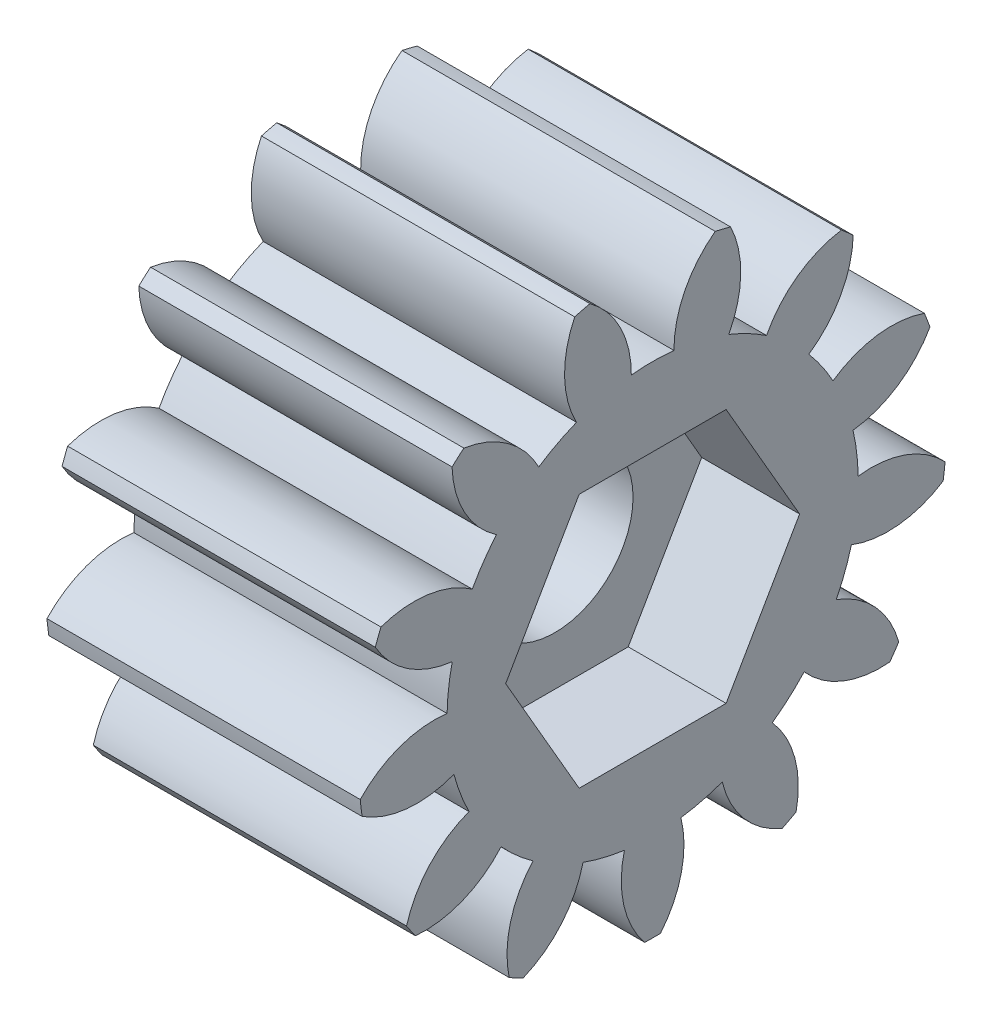
SolidWorks part; units mm, degrees
ref_plane "Plane1" through (0, 0, 0) normal (0, 0, 1) x (1, 0, 0)
ref_plane "Plane2" through (0, 0, 0) normal (0, 1, 0) x (1, 0, 0)
ref_plane "Plane3" through (0, 0, 0) normal (1, 0, 0) x (0, 0, -1)
sketch "HoldingSke" plane through (0, 0, 0) normal (0, 1, 0) x (1, 0, 0)
  line L0 (0, 0) -> (0.4872, -0.1125)
  line L1 (-15, 0) -> (100, 0) construction
  line L2 (0, 0) -> (-2.1039, 2.3779)
  line L3 (0, 0) -> (-11.863, 4.5341)
  line L4 (0, 0) -> (8.4147, 1.9427)
  line L5 (0, 0) -> (-46.8476, -17.4728)
  line L6 (0, 0) -> (-13.2634, -8.9489)
  line L7 (-2.1039, 2.3779) -> (8.6586, 51.2059)
  line L8 (-76.2, 54.61) -> (-74.8, 54.61)
  line L9 (-71.009, 38.7566) -> (-53.1078, 45.2721)
  line L10 (-76.2, 71.12) -> (104.1128, 71.12)
  line L11 (0, 0) -> (-16, 0)
  line L12 (-76.2, 101.6) -> (-76.133, 101.6)
  line L13 (24.9733, 27.94) -> (52.9518, 28.4284)
  line L14 (24.9733, 27.94) -> (24.9743, 27.94)
  line L15 (24.9733, 27.94) -> (100.4006, 29.5858)
  line L16 (-63.627, -2) -> (-12.827, -2)
  circle A0 centre (0, 0) radius 4
  circle A1 centre (0, 0) radius 10.499
  circle A2 centre (0, 0) radius 37.5
  circle A3 centre (0, 0) radius 4
  dimension "MHD" = 20.998
  dimension "Hub_dia" = 75
  dimension "Bore" = 8
  dimension "MBD" = 8
  dimension "Num_teeth" = 13
  dimension "Pitch_radius" = 180.3128
  dimension "Pitch" = 0.5
  dimension "Width" = 16
  dimension "Overall_len" = 50
  dimension "Show_teeth" = 13
  dimension "Thickness" = 16
  dimension "OAL" = 50.0001
  dimension "T_dim" = 1.4
  dimension "Ap" = 20
  dimension "H" = 19.05
  dimension "Backlash" = 0.067
  dimension "Addendum_fac" = 1
  dimension "Dedendum_fac" = 1.25
  dimension "Clearance_fac" = 0.25
  dimension "Dedendum_add" = 0.001
  dimension "Module" = 2
sketch "BasProSke" plane through (0, 0, 0) normal (0, 1, 0) x (1, 0, 0)
  line L0 (-10, 0) -> (60, 0) construction
  line L1 (0, 0) -> (0, 15)
  line L2 (0, 0) -> (16, 0)
  line L3 (16, 0) -> (16, 15)
  line L4 (16, 15) -> (0, 15)
  dimension "Diameter" = 30
  dimension "Thickness" = 16
revolve "Base-Revolve" add sketch "BasProSke" angle 360 about L0
sketch "TooCutSke" plane through (0, 0, 0) normal (1, 0, 0) x (0, 0, -1)
  line L1 (0, 0) -> (0, 107) construction
  line L2 (0, 0) -> (-1.6841, 12.8905) construction
  line L3 (0, 0) -> (-6.1834, 25.087) construction
  line L4 (-1.6841, 12.8905) -> (-3.0917, 12.5435) construction
  arc A0 (1.0882, 10.4424) -> (-1.0882, 10.4424) centre (0, 0) ccw
  arc A1 (3.2249, 14.6752) -> (-3.2249, 14.6752) centre (0, 0) ccw
  circle A2 centre (0, 0) radius 13 construction
  circle A3 centre (0, 0) radius 12.216 construction
  arc A4 (-1.0882, 10.4424) -> (-3.2249, 14.6752) centre (-6.2882, 10.4733) ccw
  arc A5 (3.2249, 14.6752) -> (1.0882, 10.4424) centre (6.2882, 10.4733) ccw
  dimension "Root_dia" = 20.998
  dimension "Overcut_dia" = 30.0508
  dimension "Pitch_dia" = 26
  dimension "Base_dia" = 24.432
  dimension "Flank_rad" = 5.2
  dimension "Half_ang" = 13.846
  dimension "Half_CT" = 1.4497
extrude "ToothCut" cut sketch "TooCutSke" along normal through all
fillet "Breaks" [suppressed] radius 0.04
fillet "RootFillets" [suppressed] radius 0.501
pattern_circular "TeethCuts" count 13 every 27.692 about axis through (-10, 0, 0) along (1, 0, 0) of "ToothCut", "RootFillets", "Breaks"
sketch "HubNeaOneSke" plane through (0, 0, 0) normal (-1, 0, 0) x (0, 0, 1)
  circle A0 centre (0, 0) radius 10.499
  dimension "Diameter" = 20.998
extrude "HubNearOne" [suppressed] add sketch "HubNeaOneSke" along normal blind 34.0001
sketch "HubNeaBotSke" plane through (0, 0, 0) normal (-1, 0, 0) x (0, 0, 1)
  circle A0 centre (0, 0) radius 10.499
  dimension "Diameter" = 20.998
extrude "HubNearBoth" [suppressed] add sketch "HubNeaBotSke" along normal blind 17
ref_plane "FarPln" through (16, 0, 0) normal (1, 0, 0) x (0, 0, -1)
sketch "HubFarSke" plane through (16, 0, 0) normal (1, 0, 0) x (0, 0, -1)
  circle A0 centre (0, 0) radius 10.499
  dimension "Diameter" = 20.998
extrude "HubFar" [suppressed] add sketch "HubFarSke" along normal blind 17
sketch "BorSke" plane through (0, 0, 0) normal (1, 0, 0) x (0, 0, -1)
  circle A0 centre (0, 0) radius 4
  dimension "Diameter" = 8
extrude "Bore" cut sketch "BorSke" along normal mid plane 100.0001
sketch "KeySke" plane through (0, 0, 0) normal (1, 0, 0) x (0, 0, -1)
  line L0 (-1.5, 0) -> (-1.5, 5.4)
  line L1 (-1.5, 5.4) -> (1.5, 5.4)
  line L2 (1.5, 5.4) -> (1.5, 0)
  line L3 (0, 0) -> (0, 34) construction
  line L4 (-1.5, 0) -> (1.5, 0)
  dimension "Offset" = 5.4
  dimension "Width" = 3
extrude "Keyway" [suppressed] cut sketch "KeySke" along normal mid plane 100.0001
pattern_circular "Keyway2" [suppressed] count 2 every 90 about axis through (-10, 0, 0) along (1, 0, 0)
sketch "Sketch1" plane through (16, 0, 0) normal (1, 0, 0) x (0, 0, -1)
  line L1 (-3.7528, 6.5) -> (-7.5056, 0)
  line L2 (-7.5056, 0) -> (-3.7528, -6.5)
  line L3 (-3.7528, -6.5) -> (3.7528, -6.5)
  line L4 (3.7528, -6.5) -> (7.5056, 0)
  line L5 (7.5056, 0) -> (3.7528, 6.5)
  line L6 (3.7528, 6.5) -> (-3.7528, 6.5)
  circle A0 centre (0, 0) radius 6.5 construction
  dimension "D1" = 13
extrude "Cut-Extrude1" cut sketch "Sketch1" against normal blind 5
equation "' \"Module@HoldingSke\" = 6.35"
equation "' \"Num_teeth@HoldingSke\" = 12"
equation "' \"Ap@HoldingSke\" =  20"
equation "' \"Width@HoldingSke\" = 0.5 * 25.4"
equation "' \"Hub_dia@HoldingSke\"= 1 * 25.4"
equation "' \"Overall_len@HoldingSke\" = 1.0 * 25.4"
equation "' \"Bore@HoldingSke\" = 0.75 * 25.4"
equation "' \"T_dim@HoldingSke\" = 0.1 * 25.4"
equation "' \"Width@KeySke\" = 0.25 * 25.4"
equation "' \"Show_teeth@HoldingSke\" = 13"
equation "' \"Backlash@HoldingSke\" = 0.009 * 25.4"
equation "' \"Addendum_fac@HoldingSke\" = 1.0"
equation "' \"Dedendum_fac@HoldingSke\" = 1.25"
equation "' \"Dedendum_add@HoldingSke\" = 0.00005 * 25.4"
equation "' \"Clearance_fac@HoldingSke\" = 0.25"
equation "\"Pitch@HoldingSke\" = 1 / \"Module@HoldingSke\""
equation "\"Overcut_dia@TooCutSke\" = (\"Num_teeth@HoldingSke\" + 2 * \"Addendum_fac@HoldingSke\") / \"Pitch@HoldingSke\" + 0.002 * 25.4"
equation "\"Pitch_dia@TooCutSke\" = \"Num_teeth@HoldingSke\" / \"Pitch@HoldingSke\""
equation "\"Base_dia@TooCutSke\" = \"Num_teeth@HoldingSke\" / \"Pitch@HoldingSke\" * cos((\"Ap@HoldingSke\"  * 3.14159265 / 180))"
equation "\"Root_dia@TooCutSke\" = (\"Num_teeth@HoldingSke\" + 2) / \"Pitch@HoldingSke\" - 2 * (\"Addendum_fac@HoldingSke\" + \"Dedendum_fac@HoldingSke\") / \"Pitch@HoldingSke\" - \"Dedendum_add@HoldingSke\" * 2"
equation "\"Half_ang@TooCutSke\" = 180 / \"Num_teeth@HoldingSke\""
equation "\"Half_CT@TooCutSke\" = \"Num_teeth@HoldingSke\" / \"Pitch@HoldingSke\" * sin((3.14159265 / 2 / \"Num_teeth@HoldingSke\")) / 2 - 7 * \"Backlash@HoldingSke\" / 4"
equation "\"Flank_rad@TooCutSke\" = \"Num_teeth@HoldingSke\" / \"Pitch@HoldingSke\" / 5"
equation "\"Radius@RootFillets\" = \"Clearance_fac@HoldingSke\" / \"Pitch@HoldingSke\" + \"Dedendum_add@HoldingSke\""
equation "\"Break_rad@Breaks\" = 0.02 / \"Pitch@HoldingSke\""
equation "\"Thickness@HoldingSke\" = \"Width@HoldingSke\""
equation "\"OAL@HoldingSke\" = \"Thickness@HoldingSke\""
equation "\"MHD@HoldingSke\" = (\"Num_teeth@HoldingSke\" + 2) / \"Pitch@HoldingSke\" - 2 * (\"Addendum_fac@HoldingSke\" + \"Dedendum_fac@HoldingSke\")  / \"Pitch@HoldingSke\" - \"Dedendum_add@HoldingSke\" * 2"
equation "\"MBD@HoldingSke\" = (\"Num_teeth@HoldingSke\" + 2) / \"Pitch@HoldingSke\" - 2 * (\"Addendum_fac@HoldingSke\" + \"Dedendum_fac@HoldingSke\")  / \"Pitch@HoldingSke\" - \"Dedendum_add@HoldingSke\" * 2 - 0.002 * 25.4"
equation "\"MHD@HoldingSke\" = ((sgn( \"MHD@HoldingSke\" - \"Hub_dia@HoldingSke\" )-1)*( \"MHD@HoldingSke\" - \"Hub_dia@HoldingSke\" ))/-2+ \"Hub_dia@HoldingSke\""
equation "\"MBD@HoldingSke\" = ((sgn( \"MBD@HoldingSke\" - \"Bore@HoldingSke\" )-1)*( \"MBD@HoldingSke\" - \"Bore@HoldingSke\" ))/-2+ \"Bore@HoldingSke\""
equation "\"OAL@HoldingSke\" = ((sgn( \"OAL@HoldingSke\" - \"Overall_len@HoldingSke\" )+1)*( \"OAL@HoldingSke\" - \"Overall_len@HoldingSke\" ))/2 + \"Overall_len@HoldingSke\" + 0.000002 * 25.4"
equation "\"Num_teeth@TeethCuts\" = int( \"Show_teeth@HoldingSke\" ) + 1"
equation "\"Num_teeth@TeethCuts\" = ((sgn( \"Num_teeth@TeethCuts\" - \"Num_teeth@HoldingSke\" )-1)*( \"Num_teeth@TeethCuts\" - \"Num_teeth@HoldingSke\" ))/-2+ \"Num_teeth@HoldingSke\""
equation "\"Num_teeth@TeethCuts\" = ((sgn( \"Num_teeth@TeethCuts\" - 2.0)+1)*( \"Num_teeth@TeethCuts\" - 2.0))/2 +2.0"
equation "\"Angle@TeethCuts\" = 360.0 / \"Num_teeth@HoldingSke\""
equation "\"Diameter@BasProSke\" = (\"Num_teeth@HoldingSke\" + 2 * \"Addendum_fac@HoldingSke\") / \"Pitch@HoldingSke\""
equation "\"Thickness@BasProSke\"  = \"Thickness@HoldingSke\""
equation "' \"Fillet_rad@BasProSke\" =  \"Thickness@HoldingSke\" * 0.05"
equation "\"MHD@HoldingSke\" = ((sgn( \"MHD@HoldingSke\" - \"Root_dia@TooCutSke\" )-1)*( \"MHD@HoldingSke\" - \"Root_dia@TooCutSke\" ))/-2+ \"Root_dia@TooCutSke\""
equation "\"Diameter@HubNeaOneSke\" = \"MHD@HoldingSke\""
equation "\"Length@HubNearOne\" = \"OAL@HoldingSke\" - \"Thickness@BasProSke\""
equation "\"Diameter@HubNeaBotSke\" = \"MHD@HoldingSke\""
equation "\"Length@HubNearBoth\" = ( \"OAL@HoldingSke\" - \"Thickness@BasProSke\" ) / 2.0"
equation "\"Thickness@FarPln\" = \"Thickness@BasProSke\""
equation "\"Diameter@HubFarSke\" = \"MHD@HoldingSke\""
equation "\"Length@HubFar\" = ( \"OAL@HoldingSke\" - \"Thickness@BasProSke\" ) / 2.0"
equation "\"Diameter@BorSke\" = \"MBD@HoldingSke\""
equation "\"D1@Bore\" = \"OAL@HoldingSke\" * 2.0"
equation "\"D1@Keyway\" = \"OAL@HoldingSke\" * 2.0"
equation "\"Offset@KeySke\" = \"T_dim@HoldingSke\" + \"MBD@HoldingSke\" / 2.0"
